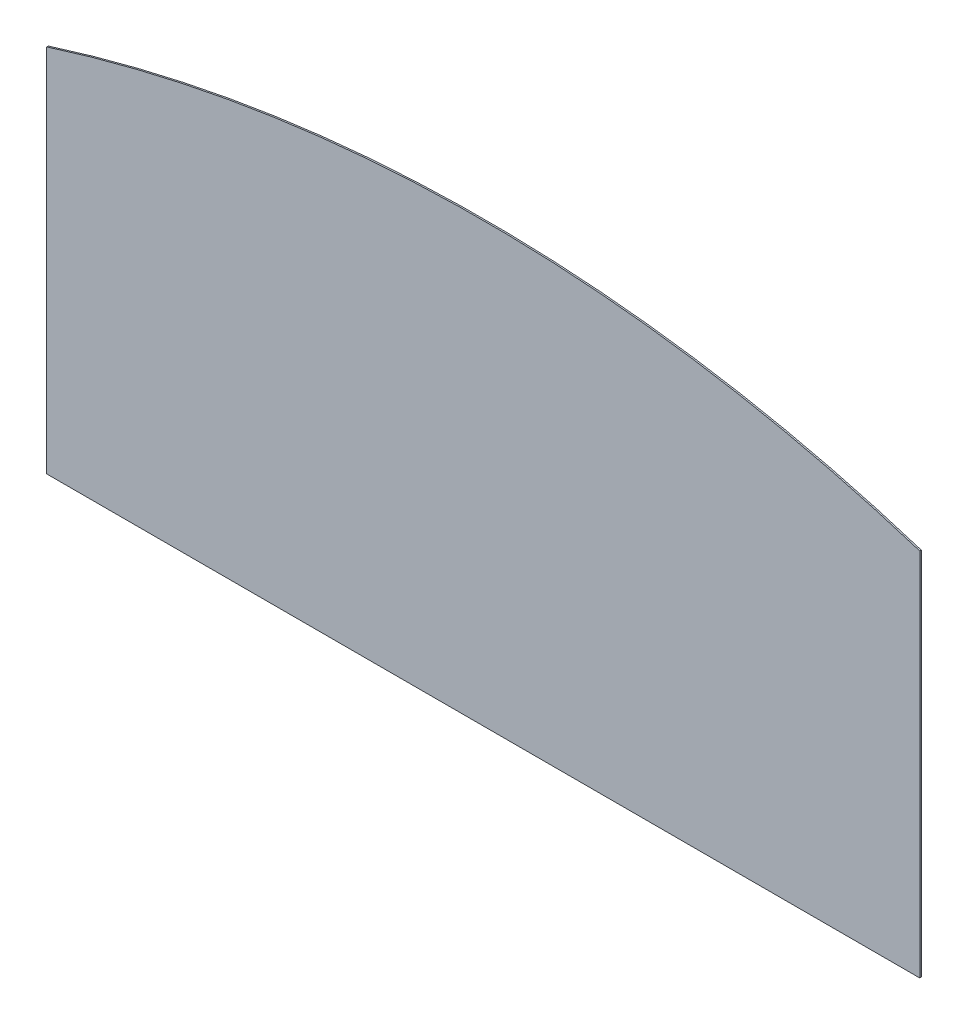
SolidWorks part; units mm, degrees
ref_plane "Front Plane" through (0, 0, 0) normal (0, 0, 1) x (1, 0, 0)
ref_plane "Top Plane" through (0, 0, 0) normal (0, 1, 0) x (1, 0, 0)
ref_plane "Right Plane" through (0, 0, 0) normal (1, 0, 0) x (0, 0, -1)
sketch "Sketch1" plane through (0, 0, 0) normal (0, 0, 1) x (1, 0, 0)
  line L0 (0, 0) -> (3657.6, 0)
  line L1 (0, 0) -> (0, 1549.4)
  line L2 (3657.6, 0) -> (3657.6, 1549.4)
  arc A0 (0, 1549.4) -> (3657.6, 1549.4) centre (1828.8, -4175.0312) cw
  point P4 (1828.8, 1828.8)
  dimension "D1" = 3657.6
  dimension "D2" = 1549.4
  dimension "D3" = 1828.8
extrude "Boss-Extrude1" add sketch "Sketch1" along normal blind 6.35
